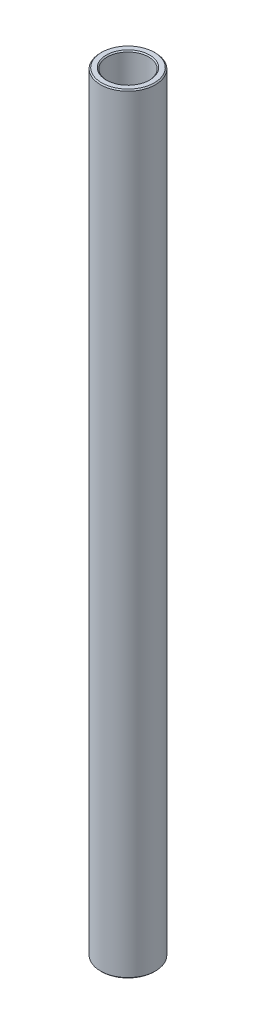
SolidWorks part; units mm, degrees
ref_plane "Front Plane" through (0, 0, 0) normal (0, 0, 1) x (1, 0, 0)
ref_plane "Top Plane" through (0, 0, 0) normal (0, 1, 0) x (1, 0, 0)
ref_plane "Right Plane" through (0, 0, 0) normal (1, 0, 0) x (0, 0, -1)
sketch "Sketch1" plane through (0, 0, 0) normal (0, 0, 1) x (1, 0, 0)
  line L0 (0, 11.6086) -> (0, -11.6086) construction
  line L1 (4.7625, 88.9) -> (6.35, 88.9)
  line L2 (6.35, 88.9) -> (6.35, -88.9)
  line L3 (6.35, -88.9) -> (4.7625, -88.9)
  line L4 (4.7625, -88.9) -> (4.7625, 88.9)
  line L5 (4.7625, 0) -> (0, 0) construction
  dimension "D1" = 9.525
  dimension "D2" = 12.7
  dimension "D3" = 177.8
revolve "Revolve1" add sketch "Sketch1" angle 360 about L0
chamfer "Chamfer1" distance 0.254 angle 45 4 edges at (-4.7625, -88.9, 0) (-6.35, -88.9, 0) (-6.35, 88.9, 0) (-4.7625, 88.9, 0)
